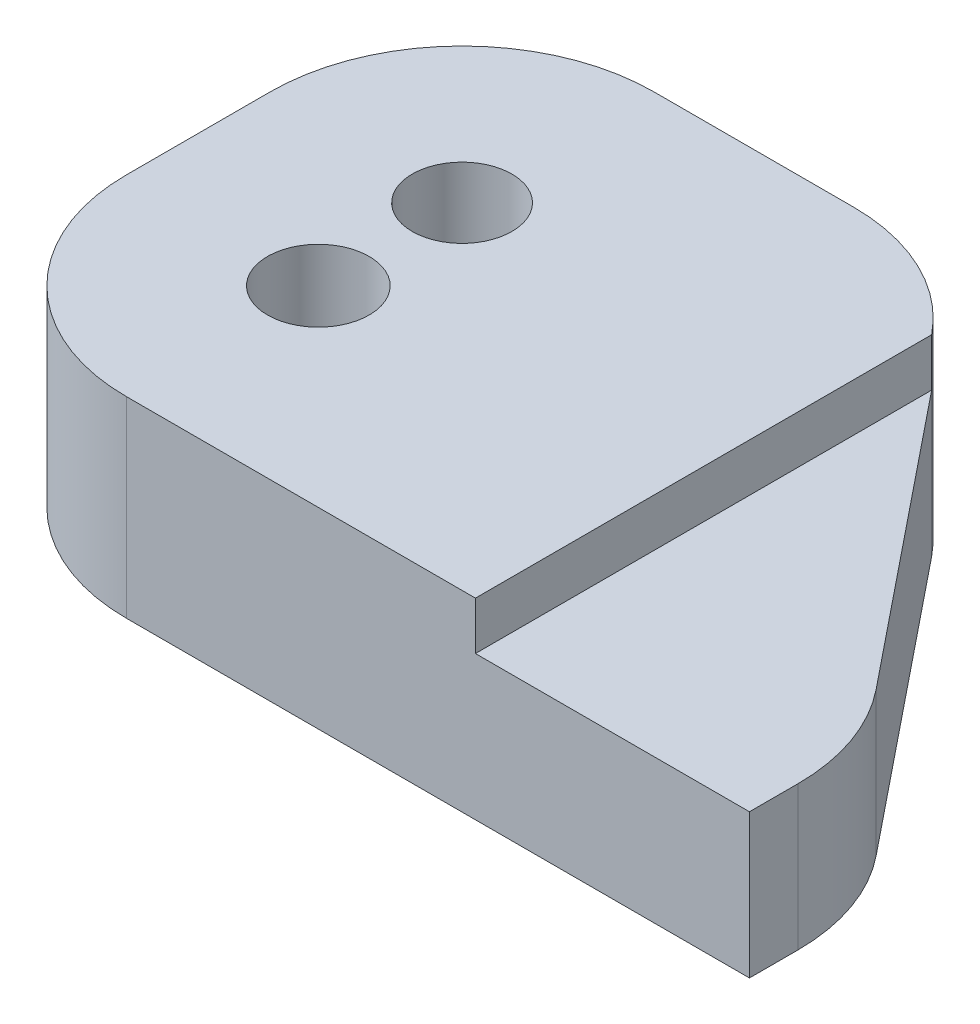
SolidWorks part; units mm, degrees
ref_plane "Front Plane" through (0, 0, 0) normal (0, 0, 1) x (1, 0, 0)
ref_plane "Top Plane" through (0, 0, 0) normal (0, 1, 0) x (1, 0, 0)
ref_plane "Right Plane" through (0, 0, 0) normal (1, 0, 0) x (0, 0, -1)
sketch "Sketch1" plane through (0, 0, 0) normal (0, 1, 0) x (1, 0, 0)
  line L0 (10.0403, 34.9076) -> (53.9179, -19.499)
  line L1 (-53.9179, -34.9076) -> (53.9179, -34.9076)
  line L2 (-53.9179, -34.9076) -> (-53.9179, 34.9076)
  line L3 (-53.9179, 34.9076) -> (10.0403, 34.9076)
  line L4 (53.9179, -34.9076) -> (53.9179, -19.499)
  line L5 (-53.9179, -34.9076) -> (53.9179, 34.9076) construction
  line L6 (-53.9179, 34.9076) -> (53.9179, -34.9076) construction
  line L7 (10.0403, 34.9076) -> (53.9179, 34.9076) construction
  line L8 (53.9179, 34.9076) -> (53.9179, -19.499) construction
  point P0 (0, 0)
extrude "Boss-Extrude1" add sketch "Sketch1" along normal blind 19.05
fillet "Fillet1" radius 25.4 4 edges at (-53.9179, 9.525, 34.9076) (-53.9179, 9.525, -34.9076) (10.0403, 9.525, -34.9076) (53.9179, 9.525, 19.499)
sketch "Sketch3" plane through (0, 19.05, 0) normal (0, 1, 0) x (1, 0, 0)
  line L0 (17.6653, 25.4528) -> (17.6653, -34.9076)
  line L5 (-53.9179, 9.5076) -> (-53.9179, -9.5076)
  line L6 (-28.5179, -34.9076) -> (53.9179, -34.9076)
  line L7 (53.9179, -34.9076) -> (53.9179, -28.4651)
  line L8 (48.2894, -12.5199) -> (17.6653, 25.4528)
  line L9 (-2.1061, 34.9076) -> (-28.5179, 34.9076)
  line L10 (-53.9179, 9.5076) -> (-53.9179, -9.5076)
  line L11 (-28.5179, -34.9076) -> (17.6653, -34.9076)
  line L14 (-2.1061, 34.9076) -> (-28.5179, 34.9076)
  arc A4 (-53.9179, -9.5076) -> (-28.5179, -34.9076) centre (-28.5179, -9.5076) ccw
  arc A5 (53.9179, -28.4651) -> (48.2894, -12.5199) centre (28.5179, -28.4651) ccw
  arc A6 (17.6653, 25.4528) -> (-2.1061, 34.9076) centre (-2.1061, 9.5076) ccw
  arc A7 (-28.5179, 34.9076) -> (-53.9179, 9.5076) centre (-28.5179, 9.5076) ccw
  arc A8 (-53.9179, -9.5076) -> (-28.5179, -34.9076) centre (-28.5179, -9.5076) ccw
  arc A10 (17.6653, 25.4528) -> (-2.1061, 34.9076) centre (-2.1061, 9.5076) ccw
  arc A11 (-28.5179, 34.9076) -> (-53.9179, 9.5076) centre (-28.5179, 9.5076) ccw
  dimension "D1" = 0
extrude "Boss-Extrude2" add sketch "Sketch3" along normal blind 6.35
sketch "Sketch4" plane through (0, 25.4, 0) normal (0, 1, 0) x (1, 0, 0)
  circle A0 centre (-28.5179, -9.5076) radius 6.7218
  circle A1 centre (-28.5179, 9.5076) radius 6.5909
extrude "Cut-Extrude3" cut sketch "Sketch4" against normal through all
